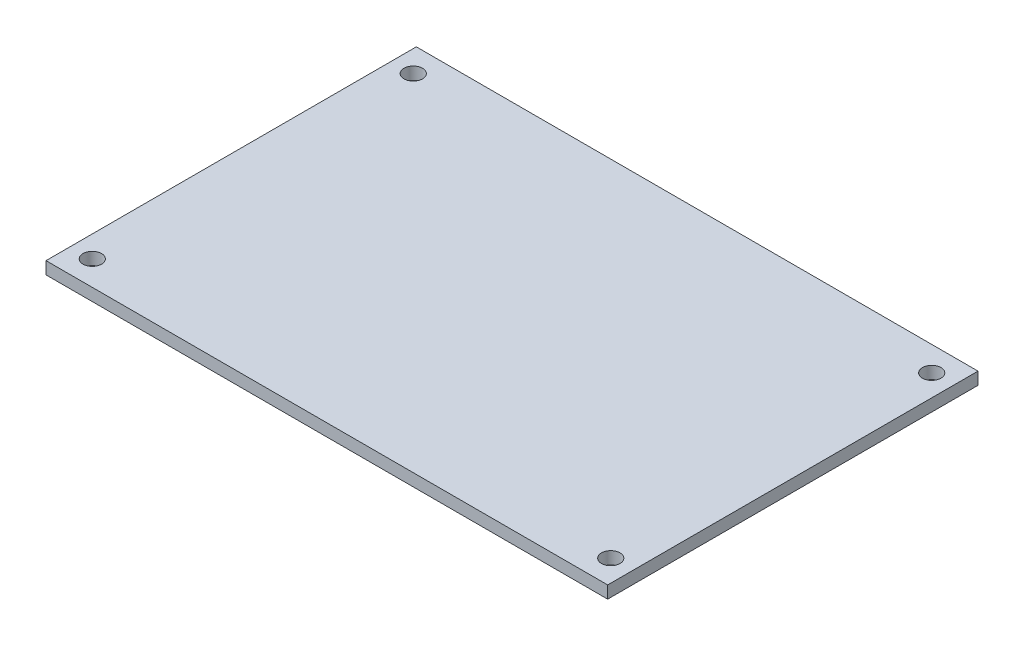
SolidWorks part; units mm, degrees
ref_plane "前视基准面" through (0, 0, 0) normal (0, 0, 1) x (1, 0, 0)
ref_plane "上视基准面" through (0, 0, 0) normal (0, 1, 0) x (1, 0, 0)
ref_plane "右视基准面" through (0, 0, 0) normal (1, 0, 0) x (0, 0, -1)
sketch "草图2" plane through (0, 0, 0) normal (0, 1, 0) x (1, 0, 0)
  line L1 (-45.5, 30) -> (45.5, 30)
  line L2 (-45.5, 30) -> (-45.5, -30)
  line L3 (-45.5, -30) -> (45.5, -30)
  line L4 (45.5, 30) -> (45.5, -30)
  line L5 (-45.5, 30) -> (45.5, -30) construction
  line L6 (-45.5, -30) -> (45.5, 30) construction
  point P0 (0, 0)
  dimension "D1" = 91
  dimension "D2" = 60
extrude "凸台-拉伸1" add sketch "草图2" along normal blind 2
sketch "草图3" plane through (0, 2, 0) normal (0, 1, 0) x (1, 0, 0)
  line L0 (55.6033, 0) -> (0, 0) construction
  line L1 (0, 0) -> (0, 53.5783) construction
  circle A0 centre (-42, 26) radius 1.5
  circle A1 centre (42, 26) radius 1.5
  circle A2 centre (-42, -26) radius 1.5
  circle A3 centre (42, -26) radius 1.5
  dimension "D1" = 3
  dimension "D3" = 52
  dimension "D2" = 84
extrude "切除-拉伸1" cut sketch "草图3" against normal blind 2
sketch "草图4" plane through (0, 0, 0) normal (0, -1, 0) x (1, 0, 0)
  text T0 "电机驱动\r\n" font "汉仪长仿宋体" height 7
